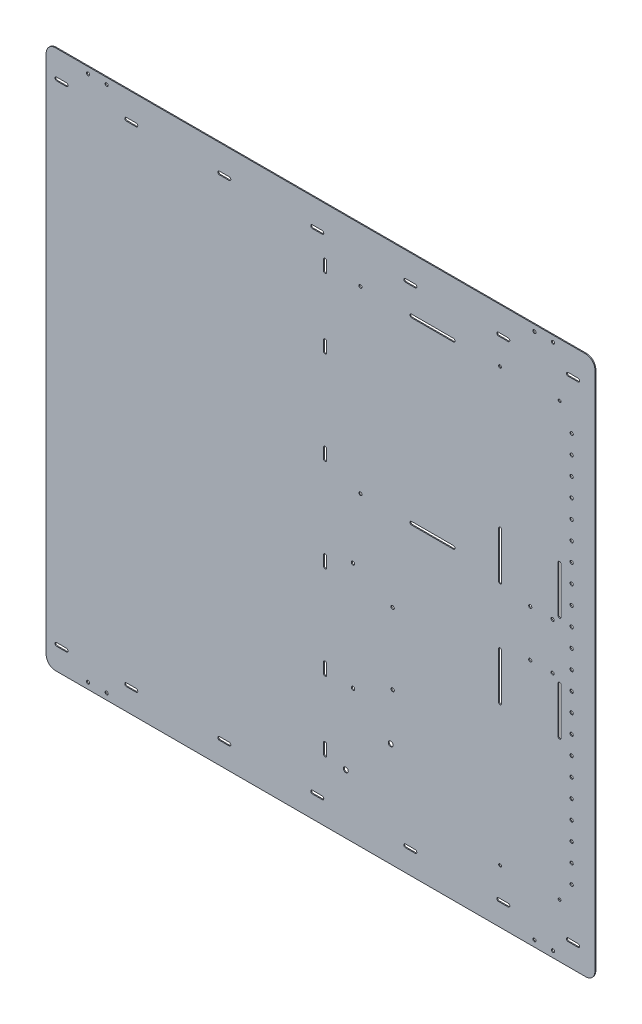
SolidWorks part; units mm, degrees
ref_plane "Front Plane" through (0, 0, 0) normal (0, 0, 1) x (1, 0, 0)
ref_plane "Top Plane" through (0, 0, 0) normal (0, 1, 0) x (1, 0, 0)
ref_plane "Right Plane" through (0, 0, 0) normal (1, 0, 0) x (0, 0, -1)
sketch "Sketch1" plane through (0, 0, 0) normal (0, 0, 1) x (1, 0, 0)
  line L1 (-295, 290) -> (295, 290)
  line L2 (-295, 290) -> (-295, -290)
  line L3 (-295, -290) -> (295, -290)
  line L4 (295, 290) -> (295, -290)
  line L5 (-295, 290) -> (295, -290) construction
  line L6 (-295, -290) -> (295, 290) construction
  point P0 (0, 0)
  dimension "D1" = 590
  dimension "D2" = 580
extrude "Boss-Extrude1" add sketch "Sketch1" along normal blind 1
hole_wizard "M3 Clearance Hole1" positions "Sketch7" profile "Sketch8" hole size "M3" standard "ANSI Metric"
sketch "Sketch7" plane through (0, 0, 0) normal (0, 0, -1) x (-1, 0, 0)
  line L2 (-250, 283.26) -> (250, 283.26)
  line L3 (-250, 283.26) -> (-250, -283.26)
  line L4 (-250, -283.26) -> (250, -283.26)
  line L5 (250, 283.26) -> (250, -283.26)
  line L6 (-250, 283.26) -> (250, -283.26) construction
  line L7 (-250, -283.26) -> (250, 283.26) construction
  line L13 (295, 290) -> (295, -290) construction
  line L14 (-230, -283.26) -> (-230, 283.26)
  line L16 (230, -283.26) -> (230, 283.26)
  point P7 (0, 0)
  point P8 (250, -283.26)
  point P155 (-250, 283.26)
  point P156 (-250, -283.26)
  point P157 (250, 283.26)
  point P212 (-230, 283.26)
  point P215 (-230, -283.26)
  point P218 (230, -283.26)
  point P221 (230, 283.26)
  dimension "D1" = 566.52
  dimension "D2" = 45
  dimension "D3" = 20
  dimension "D4" = 20
sketch "Sketch8" plane through (-230, 283.26, 0) normal (1, 0, 0) x (0, 1, 0)
  line L0 (0, 0) -> (0, 1)
  line L1 (0, 1) -> (1.7, 1)
  line L2 (1.7, 1) -> (1.7, 0.025)
  line L3 (1.7, 0.025) -> (1.725, 0)
  line L5 (1.725, 0) -> (0, 0)
  line L6 (-1.7, 0.025) -> (-1.725, 0) construction
  line L11 (0, -6.35) -> (0, 107.95) construction
  dimension "Thru Hole Dia." = 3.4
  dimension "Thru Hole Depth" = 1
  dimension "Near C'Sink Dia." = 3.45
  dimension "Near C'Sink Angle" = 90
fillet "Fillet1" radius 10 4 edges at (295, -290, 0.5) (-295, -290, 0.5) (-295, 290, 0.5) (295, 290, 0.5)
sketch "Sketch9" plane through (0, 0, 0) normal (0, 0, 1) x (1, 0, 0)
  circle A5 centre (77.5, -126.46) radius 1.8 construction
  circle A6 centre (77.5, -49.96) radius 1.8 construction
  circle A7 centre (34.9, -29.96) radius 1.8 construction
  circle A8 centre (34.9, -146.46) radius 1.8 construction
  circle A9 centre (77.5, -126.46) radius 1.8
  circle A10 centre (77.5, -49.96) radius 1.8
  circle A11 centre (34.9, -29.96) radius 1.8
  circle A12 centre (34.9, -146.46) radius 1.8
extrude "BMS Holes" cut sketch "Sketch9" along normal through all
sketch "Sketch10" plane through (0, 0, 1) normal (0, 0, 1) x (1, 0, 0)
  line L0 (292.75, 264.81) -> (295, 264.81) construction
  line L1 (-208.75, 261.56) -> (-198.25, 261.56) construction
  line L2 (273.25, 263.81) -> (269.75, 263.81)
  line L3 (269.75, 259.31) -> (273.25, 259.31)
  line L4 (-208.75, 263.31) -> (-198.25, 263.31)
  line L5 (-208.75, 259.81) -> (-198.25, 259.81)
  line L6 (-108.75, 261.56) -> (-98.25, 261.56) construction
  line L7 (-108.75, 263.31) -> (-98.25, 263.31)
  line L12 (-108.75, 259.81) -> (-98.25, 259.81)
  line L13 (-8.75, 261.56) -> (1.75, 261.56) construction
  line L14 (-8.75, 263.31) -> (1.75, 263.31)
  line L15 (-8.75, 259.81) -> (1.75, 259.81)
  line L20 (91.25, 261.56) -> (101.75, 261.56) construction
  line L21 (91.25, 263.31) -> (101.75, 263.31)
  line L22 (91.25, 259.81) -> (101.75, 259.81)
  line L23 (191.25, 261.56) -> (201.75, 261.56) construction
  line L28 (191.25, 263.31) -> (201.75, 263.31)
  line L29 (191.25, 259.81) -> (201.75, 259.81)
  line L30 (-108.75, -264.96) -> (-98.25, -264.96) construction
  line L31 (-108.75, -263.21) -> (-98.25, -263.21)
  line L36 (-108.75, -266.71) -> (-98.25, -266.71)
  line L37 (-8.75, -264.96) -> (1.75, -264.96) construction
  line L38 (-8.75, -263.21) -> (1.75, -263.21)
  line L39 (-8.75, -266.71) -> (1.75, -266.71)
  line L44 (91.25, -264.96) -> (101.75, -264.96) construction
  line L45 (91.25, -263.21) -> (101.75, -263.21)
  line L46 (91.25, -266.71) -> (101.75, -266.71)
  line L47 (191.25, -264.96) -> (201.75, -264.96) construction
  line L52 (273.25, 263.81) -> (269.75, 263.81) construction
  line L53 (269.75, 259.31) -> (273.25, 259.31) construction
  line L54 (191.25, -263.21) -> (201.75, -263.21)
  line L55 (191.25, -266.71) -> (201.75, -266.71)
  line L58 (-208.75, -264.96) -> (-198.25, -264.96) construction
  line L59 (-208.75, -263.21) -> (-198.25, -263.21)
  line L62 (-199.75, 264.81) -> (-207.25, 264.81)
  line L63 (-207.25, 258.31) -> (-199.75, 258.31)
  line L64 (-199.75, 264.81) -> (-207.25, 264.81) construction
  line L65 (-207.25, 258.31) -> (-199.75, 258.31) construction
  line L66 (-208.75, -266.71) -> (-198.25, -266.71)
  line L67 (-283.75, 261.56) -> (-273.25, 261.56) construction
  line L70 (-283.75, 263.31) -> (-273.25, 263.31)
  line L71 (-283.75, 259.81) -> (-273.25, 259.81)
  line L74 (100.25, 264.81) -> (92.75, 264.81)
  line L75 (92.75, 258.31) -> (100.25, 258.31)
  line L76 (100.25, 264.81) -> (92.75, 264.81) construction
  line L77 (92.75, 258.31) -> (100.25, 258.31) construction
  line L78 (-208.75, 261.56) -> (-283.75, 261.56) construction
  line L79 (266.25, 261.56) -> (276.75, 261.56) construction
  line L82 (266.25, 263.31) -> (276.75, 263.31)
  line L83 (266.25, 259.81) -> (276.75, 259.81)
  line L86 (200.25, 264.81) -> (192.75, 264.81)
  line L87 (192.75, 258.31) -> (200.25, 258.31)
  line L88 (200.25, 264.81) -> (192.75, 264.81) construction
  line L89 (192.75, 258.31) -> (200.25, 258.31) construction
  line L90 (266.25, -264.96) -> (276.75, -264.96) construction
  line L91 (266.25, -263.21) -> (276.75, -263.21)
  line L94 (266.25, -266.71) -> (276.75, -266.71)
  line L95 (-283.75, -264.96) -> (-273.25, -264.96) construction
  line L98 (-99.75, 264.81) -> (-107.25, 264.81)
  line L99 (-107.25, 258.31) -> (-99.75, 258.31)
  line L100 (-99.75, 264.81) -> (-107.25, 264.81) construction
  line L101 (-107.25, 258.31) -> (-99.75, 258.31) construction
  line L102 (-276.75, 263.81) -> (-280.25, 263.81)
  line L103 (-280.25, 259.31) -> (-276.75, 259.31)
  line L104 (-276.75, 263.81) -> (-280.25, 263.81) construction
  line L105 (-280.25, 259.31) -> (-276.75, 259.31) construction
  line L106 (-283.75, -263.21) -> (-273.25, -263.21)
  line L107 (-283.75, -266.71) -> (-273.25, -266.71)
  line L110 (0.25, 264.81) -> (-7.25, 264.81)
  line L111 (-7.25, 258.31) -> (0.25, 258.31)
  line L112 (0.25, 264.81) -> (-7.25, 264.81) construction
  line L113 (-7.25, 258.31) -> (0.25, 258.31) construction
  line L114 (-283.75, 261.56) -> (266.25, 261.56) construction
  line L115 (4.9, 162.1) -> (4.9, 151.6) construction
  line L118 (6.65, 162.1) -> (6.65, 151.6)
  line L119 (3.15, 162.1) -> (3.15, 151.6)
  line L120 (4.9, 62.1) -> (4.9, 51.6) construction
  line L121 (6.65, 62.1) -> (6.65, 51.6)
  line L122 (3.15, 62.1) -> (3.15, 51.6)
  line L123 (4.9, -37.9) -> (4.9, -48.4) construction
  line L128 (6.65, -37.9) -> (6.65, -48.4)
  line L129 (3.15, -37.9) -> (3.15, -48.4)
  line L130 (4.9, -137.9) -> (4.9, -148.4) construction
  line L131 (6.65, -137.9) -> (6.65, -148.4)
  line L136 (3.15, -137.9) -> (3.15, -148.4)
  line L137 (4.9, 237.1) -> (4.9, 226.6) construction
  line L138 (6.65, 237.1) -> (6.65, 226.6)
  line L139 (3.15, 237.1) -> (3.15, 226.6)
  line L144 (4.9, 162.1) -> (4.9, 237.1) construction
  line L145 (4.9, -212.9) -> (4.9, -223.4) construction
  line L146 (6.65, -212.9) -> (6.65, -223.4)
  line L147 (3.15, -212.9) -> (3.15, -223.4)
  line L152 (4.9, 237.1) -> (4.9, -212.9) construction
  line L178 (-199.75, -261.71) -> (-207.25, -261.71)
  line L179 (-207.25, -268.21) -> (-199.75, -268.21)
  line L180 (-199.75, -261.71) -> (-207.25, -261.71) construction
  line L181 (-207.25, -268.21) -> (-199.75, -268.21) construction
  line L190 (100.25, -261.71) -> (92.75, -261.71)
  line L191 (92.75, -268.21) -> (100.25, -268.21)
  line L192 (100.25, -261.71) -> (92.75, -261.71) construction
  line L193 (92.75, -268.21) -> (100.25, -268.21) construction
  line L202 (200.25, -261.71) -> (192.75, -261.71)
  line L203 (192.75, -268.21) -> (200.25, -268.21)
  line L204 (200.25, -261.71) -> (192.75, -261.71) construction
  line L205 (192.75, -268.21) -> (200.25, -268.21) construction
  line L214 (-99.75, -261.71) -> (-107.25, -261.71)
  line L215 (-107.25, -268.21) -> (-99.75, -268.21)
  line L216 (-99.75, -261.71) -> (-107.25, -261.71) construction
  line L217 (-107.25, -268.21) -> (-99.75, -268.21) construction
  line L218 (-276.75, -262.71) -> (-280.25, -262.71)
  line L219 (-280.25, -267.21) -> (-276.75, -267.21)
  line L220 (-276.75, -262.71) -> (-280.25, -262.71) construction
  line L221 (-280.25, -267.21) -> (-276.75, -267.21) construction
  line L226 (0.25, -261.71) -> (-7.25, -261.71)
  line L227 (-7.25, -268.21) -> (0.25, -268.21)
  line L228 (0.25, -261.71) -> (-7.25, -261.71) construction
  line L229 (-7.25, -268.21) -> (0.25, -268.21) construction
  line L234 (7.15, -219.9) -> (7.15, -216.4)
  line L235 (2.65, -216.4) -> (2.65, -219.9)
  line L276 (7.15, -219.9) -> (7.15, -216.4) construction
  line L277 (2.65, -216.4) -> (2.65, -219.9) construction
  line L290 (8.15, -46.9) -> (8.15, -39.4)
  line L291 (1.65, -39.4) -> (1.65, -46.9)
  line L292 (8.15, -46.9) -> (8.15, -39.4) construction
  line L293 (1.65, -39.4) -> (1.65, -46.9) construction
  line L302 (8.15, -146.9) -> (8.15, -139.4)
  line L303 (1.65, -139.4) -> (1.65, -146.9)
  line L304 (8.15, -146.9) -> (8.15, -139.4) construction
  line L305 (1.65, -139.4) -> (1.65, -146.9) construction
  line L314 (8.15, 153.1) -> (8.15, 160.6)
  line L315 (1.65, 160.6) -> (1.65, 153.1)
  line L316 (8.15, 153.1) -> (8.15, 160.6) construction
  line L317 (1.65, 160.6) -> (1.65, 153.1) construction
  line L322 (8.15, 53.1) -> (8.15, 60.6)
  line L323 (1.65, 60.6) -> (1.65, 53.1)
  line L324 (8.15, 53.1) -> (8.15, 60.6) construction
  line L325 (1.65, 60.6) -> (1.65, 53.1) construction
  line L326 (7.15, 230.1) -> (7.15, 233.6)
  line L327 (2.65, 233.6) -> (2.65, 230.1)
  line L328 (7.15, 230.1) -> (7.15, 233.6) construction
  line L329 (2.65, 233.6) -> (2.65, 230.1) construction
  line L334 (295, 258.31) -> (292.75, 258.31) construction
  line L335 (8.15, -239.4) -> (8.15, -241.65) construction
  line L341 (1.65, -241.65) -> (1.65, -239.4) construction
  line L342 (292.75, -261.71) -> (295, -261.71) construction
  line L348 (295, -268.21) -> (292.75, -268.21) construction
  line L349 (292.75, 264.81) -> (295, 264.81) construction
  line L355 (295, 258.31) -> (292.75, 258.31) construction
  line L356 (8.15, -239.4) -> (8.15, -241.65) construction
  line L362 (1.65, -241.65) -> (1.65, -239.4) construction
  line L363 (292.75, -261.71) -> (295, -261.71) construction
  line L369 (295, -268.21) -> (292.75, -268.21) construction
  arc A0 (292.75, 264.81) -> (292.75, 258.31) centre (292.75, 261.56) ccw construction
  arc A1 (8.15, -239.4) -> (1.65, -239.4) centre (4.9, -239.4) ccw construction
  arc A2 (273.25, 259.31) -> (273.25, 263.81) centre (273.25, 261.56) ccw
  arc A3 (269.75, 263.81) -> (269.75, 259.31) centre (269.75, 261.56) ccw
  arc A4 (-208.75, 263.31) -> (-208.75, 259.81) centre (-208.75, 261.56) ccw
  arc A5 (-198.25, 259.81) -> (-198.25, 263.31) centre (-198.25, 261.56) ccw
  arc A6 (-108.75, 263.31) -> (-108.75, 259.81) centre (-108.75, 261.56) ccw
  arc A7 (-98.25, 259.81) -> (-98.25, 263.31) centre (-98.25, 261.56) ccw
  arc A12 (-8.75, 263.31) -> (-8.75, 259.81) centre (-8.75, 261.56) ccw
  arc A13 (1.75, 259.81) -> (1.75, 263.31) centre (1.75, 261.56) ccw
  arc A14 (91.25, 263.31) -> (91.25, 259.81) centre (91.25, 261.56) ccw
  arc A15 (101.75, 259.81) -> (101.75, 263.31) centre (101.75, 261.56) ccw
  arc A20 (191.25, 263.31) -> (191.25, 259.81) centre (191.25, 261.56) ccw
  arc A21 (201.75, 259.81) -> (201.75, 263.31) centre (201.75, 261.56) ccw
  arc A22 (-108.75, -263.21) -> (-108.75, -266.71) centre (-108.75, -264.96) ccw
  arc A23 (-98.25, -266.71) -> (-98.25, -263.21) centre (-98.25, -264.96) ccw
  arc A28 (-8.75, -263.21) -> (-8.75, -266.71) centre (-8.75, -264.96) ccw
  arc A29 (1.75, -266.71) -> (1.75, -263.21) centre (1.75, -264.96) ccw
  arc A30 (91.25, -263.21) -> (91.25, -266.71) centre (91.25, -264.96) ccw
  arc A31 (101.75, -266.71) -> (101.75, -263.21) centre (101.75, -264.96) ccw
  arc A36 (191.25, -263.21) -> (191.25, -266.71) centre (191.25, -264.96) ccw
  arc A37 (201.75, -266.71) -> (201.75, -263.21) centre (201.75, -264.96) ccw
  arc A38 (-208.75, -263.21) -> (-208.75, -266.71) centre (-208.75, -264.96) ccw
  arc A39 (-198.25, -266.71) -> (-198.25, -263.21) centre (-198.25, -264.96) ccw
  arc A44 (-283.75, 263.31) -> (-283.75, 259.81) centre (-283.75, 261.56) ccw
  arc A45 (-273.25, 259.81) -> (-273.25, 263.31) centre (-273.25, 261.56) ccw
  arc A46 (266.25, 263.31) -> (266.25, 259.81) centre (266.25, 261.56) ccw
  arc A47 (276.75, 259.81) -> (276.75, 263.31) centre (276.75, 261.56) ccw
  arc A52 (273.25, 259.31) -> (273.25, 263.81) centre (273.25, 261.56) ccw construction
  arc A53 (269.75, 263.81) -> (269.75, 259.31) centre (269.75, 261.56) ccw construction
  arc A54 (266.25, -263.21) -> (266.25, -266.71) centre (266.25, -264.96) ccw
  arc A55 (276.75, -266.71) -> (276.75, -263.21) centre (276.75, -264.96) ccw
  arc A58 (-283.75, -263.21) -> (-283.75, -266.71) centre (-283.75, -264.96) ccw
  arc A59 (-273.25, -266.71) -> (-273.25, -263.21) centre (-273.25, -264.96) ccw
  arc A62 (-199.75, 258.31) -> (-199.75, 264.81) centre (-199.75, 261.56) ccw
  arc A63 (-207.25, 264.81) -> (-207.25, 258.31) centre (-207.25, 261.56) ccw
  arc A64 (-199.75, 258.31) -> (-199.75, 264.81) centre (-199.75, 261.56) ccw construction
  arc A65 (-207.25, 264.81) -> (-207.25, 258.31) centre (-207.25, 261.56) ccw construction
  arc A66 (6.65, 162.1) -> (3.15, 162.1) centre (4.9, 162.1) ccw
  arc A67 (3.15, 151.6) -> (6.65, 151.6) centre (4.9, 151.6) ccw
  arc A70 (6.65, 62.1) -> (3.15, 62.1) centre (4.9, 62.1) ccw
  arc A71 (3.15, 51.6) -> (6.65, 51.6) centre (4.9, 51.6) ccw
  arc A74 (100.25, 258.31) -> (100.25, 264.81) centre (100.25, 261.56) ccw
  arc A75 (92.75, 264.81) -> (92.75, 258.31) centre (92.75, 261.56) ccw
  arc A76 (100.25, 258.31) -> (100.25, 264.81) centre (100.25, 261.56) ccw construction
  arc A77 (92.75, 264.81) -> (92.75, 258.31) centre (92.75, 261.56) ccw construction
  arc A78 (6.65, -37.9) -> (3.15, -37.9) centre (4.9, -37.9) ccw
  arc A79 (3.15, -48.4) -> (6.65, -48.4) centre (4.9, -48.4) ccw
  arc A82 (6.65, -137.9) -> (3.15, -137.9) centre (4.9, -137.9) ccw
  arc A83 (3.15, -148.4) -> (6.65, -148.4) centre (4.9, -148.4) ccw
  arc A86 (200.25, 258.31) -> (200.25, 264.81) centre (200.25, 261.56) ccw
  arc A87 (192.75, 264.81) -> (192.75, 258.31) centre (192.75, 261.56) ccw
  arc A88 (200.25, 258.31) -> (200.25, 264.81) centre (200.25, 261.56) ccw construction
  arc A89 (192.75, 264.81) -> (192.75, 258.31) centre (192.75, 261.56) ccw construction
  arc A90 (6.65, 237.1) -> (3.15, 237.1) centre (4.9, 237.1) ccw
  arc A91 (3.15, 226.6) -> (6.65, 226.6) centre (4.9, 226.6) ccw
  arc A94 (6.65, -212.9) -> (3.15, -212.9) centre (4.9, -212.9) ccw
  arc A95 (3.15, -223.4) -> (6.65, -223.4) centre (4.9, -223.4) ccw
  arc A98 (-99.75, 258.31) -> (-99.75, 264.81) centre (-99.75, 261.56) ccw
  arc A99 (-107.25, 264.81) -> (-107.25, 258.31) centre (-107.25, 261.56) ccw
  arc A100 (-99.75, 258.31) -> (-99.75, 264.81) centre (-99.75, 261.56) ccw construction
  arc A101 (-107.25, 264.81) -> (-107.25, 258.31) centre (-107.25, 261.56) ccw construction
  arc A102 (-276.75, 259.31) -> (-276.75, 263.81) centre (-276.75, 261.56) ccw
  arc A103 (-280.25, 263.81) -> (-280.25, 259.31) centre (-280.25, 261.56) ccw
  arc A104 (-276.75, 259.31) -> (-276.75, 263.81) centre (-276.75, 261.56) ccw construction
  arc A105 (-280.25, 263.81) -> (-280.25, 259.31) centre (-280.25, 261.56) ccw construction
  arc A110 (0.25, 258.31) -> (0.25, 264.81) centre (0.25, 261.56) ccw
  arc A111 (-7.25, 264.81) -> (-7.25, 258.31) centre (-7.25, 261.56) ccw
  arc A112 (0.25, 258.31) -> (0.25, 264.81) centre (0.25, 261.56) ccw construction
  arc A113 (-7.25, 264.81) -> (-7.25, 258.31) centre (-7.25, 261.56) ccw construction
  arc A178 (-199.75, -268.21) -> (-199.75, -261.71) centre (-199.75, -264.96) ccw
  arc A179 (-207.25, -261.71) -> (-207.25, -268.21) centre (-207.25, -264.96) ccw
  arc A180 (-199.75, -268.21) -> (-199.75, -261.71) centre (-199.75, -264.96) ccw construction
  arc A181 (-207.25, -261.71) -> (-207.25, -268.21) centre (-207.25, -264.96) ccw construction
  arc A190 (100.25, -268.21) -> (100.25, -261.71) centre (100.25, -264.96) ccw
  arc A191 (92.75, -261.71) -> (92.75, -268.21) centre (92.75, -264.96) ccw
  arc A192 (100.25, -268.21) -> (100.25, -261.71) centre (100.25, -264.96) ccw construction
  arc A193 (92.75, -261.71) -> (92.75, -268.21) centre (92.75, -264.96) ccw construction
  arc A202 (200.25, -268.21) -> (200.25, -261.71) centre (200.25, -264.96) ccw
  arc A203 (192.75, -261.71) -> (192.75, -268.21) centre (192.75, -264.96) ccw
  arc A204 (200.25, -268.21) -> (200.25, -261.71) centre (200.25, -264.96) ccw construction
  arc A205 (192.75, -261.71) -> (192.75, -268.21) centre (192.75, -264.96) ccw construction
  arc A214 (-99.75, -268.21) -> (-99.75, -261.71) centre (-99.75, -264.96) ccw
  arc A215 (-107.25, -261.71) -> (-107.25, -268.21) centre (-107.25, -264.96) ccw
  arc A216 (-99.75, -268.21) -> (-99.75, -261.71) centre (-99.75, -264.96) ccw construction
  arc A217 (-107.25, -261.71) -> (-107.25, -268.21) centre (-107.25, -264.96) ccw construction
  arc A218 (-276.75, -267.21) -> (-276.75, -262.71) centre (-276.75, -264.96) ccw
  arc A219 (-280.25, -262.71) -> (-280.25, -267.21) centre (-280.25, -264.96) ccw
  arc A220 (-276.75, -267.21) -> (-276.75, -262.71) centre (-276.75, -264.96) ccw construction
  arc A221 (-280.25, -262.71) -> (-280.25, -267.21) centre (-280.25, -264.96) ccw construction
  arc A226 (0.25, -268.21) -> (0.25, -261.71) centre (0.25, -264.96) ccw
  arc A227 (-7.25, -261.71) -> (-7.25, -268.21) centre (-7.25, -264.96) ccw
  arc A228 (0.25, -268.21) -> (0.25, -261.71) centre (0.25, -264.96) ccw construction
  arc A229 (-7.25, -261.71) -> (-7.25, -268.21) centre (-7.25, -264.96) ccw construction
  arc A234 (2.65, -219.9) -> (7.15, -219.9) centre (4.9, -219.9) ccw
  arc A235 (7.15, -216.4) -> (2.65, -216.4) centre (4.9, -216.4) ccw
  arc A276 (2.65, -219.9) -> (7.15, -219.9) centre (4.9, -219.9) ccw construction
  arc A277 (7.15, -216.4) -> (2.65, -216.4) centre (4.9, -216.4) ccw construction
  arc A290 (1.65, -46.9) -> (8.15, -46.9) centre (4.9, -46.9) ccw
  arc A291 (8.15, -39.4) -> (1.65, -39.4) centre (4.9, -39.4) ccw
  arc A292 (1.65, -46.9) -> (8.15, -46.9) centre (4.9, -46.9) ccw construction
  arc A293 (8.15, -39.4) -> (1.65, -39.4) centre (4.9, -39.4) ccw construction
  arc A302 (1.65, -146.9) -> (8.15, -146.9) centre (4.9, -146.9) ccw
  arc A303 (8.15, -139.4) -> (1.65, -139.4) centre (4.9, -139.4) ccw
  arc A304 (1.65, -146.9) -> (8.15, -146.9) centre (4.9, -146.9) ccw construction
  arc A305 (8.15, -139.4) -> (1.65, -139.4) centre (4.9, -139.4) ccw construction
  arc A314 (1.65, 153.1) -> (8.15, 153.1) centre (4.9, 153.1) ccw
  arc A315 (8.15, 160.6) -> (1.65, 160.6) centre (4.9, 160.6) ccw
  arc A316 (1.65, 153.1) -> (8.15, 153.1) centre (4.9, 153.1) ccw construction
  arc A317 (8.15, 160.6) -> (1.65, 160.6) centre (4.9, 160.6) ccw construction
  arc A322 (1.65, 53.1) -> (8.15, 53.1) centre (4.9, 53.1) ccw
  arc A323 (8.15, 60.6) -> (1.65, 60.6) centre (4.9, 60.6) ccw
  arc A324 (1.65, 53.1) -> (8.15, 53.1) centre (4.9, 53.1) ccw construction
  arc A325 (8.15, 60.6) -> (1.65, 60.6) centre (4.9, 60.6) ccw construction
  arc A326 (2.65, 230.1) -> (7.15, 230.1) centre (4.9, 230.1) ccw
  arc A327 (7.15, 233.6) -> (2.65, 233.6) centre (4.9, 233.6) ccw
  arc A328 (2.65, 230.1) -> (7.15, 230.1) centre (4.9, 230.1) ccw construction
  arc A329 (7.15, 233.6) -> (2.65, 233.6) centre (4.9, 233.6) ccw construction
  arc A330 (292.75, -261.71) -> (292.75, -268.21) centre (292.75, -264.96) ccw construction
  arc A331 (292.75, 264.81) -> (292.75, 258.31) centre (292.75, 261.56) ccw construction
  arc A332 (8.15, -239.4) -> (1.65, -239.4) centre (4.9, -239.4) ccw construction
  arc A333 (292.75, -261.71) -> (292.75, -268.21) centre (292.75, -264.96) ccw construction
  point P3 (-203.5, 261.56)
  point P12 (-103.5, 261.56)
  point P19 (-3.5, 261.56)
  point P26 (96.5, 261.56)
  point P33 (196.5, 261.56)
  point P40 (-103.5, -264.96)
  point P47 (-3.5, -264.96)
  point P54 (96.5, -264.96)
  point P61 (196.5, -264.96)
  point P69 (-203.5, -264.96)
  point P76 (-278.5, 261.56)
  point P88 (4.9, 156.85)
  point P90 (271.5, 261.56)
  point P102 (271.5, -264.96)
  point P115 (-278.5, -264.96)
  point P134 (4.9, 231.85)
  point P136 (4.9, 56.85)
  point P144 (4.9, -43.15)
  point P164 (4.9, -143.15)
  point P183 (4.9, -218.15)
  dimension "D8" = 3.5
  dimension "D9" = 5
  dimension "D12" = 2
  dimension "D21" = 4
  dimension "D23" = 2
  dimension "D14" = 75
  dimension "D18" = 550
  dimension "D24" = 75
  dimension "D26" = 450
  dimension "D7" = 0
  dimension "D10" = 0
  dimension "D11" = 2
  dimension "D13" = 0
  dimension "D15" = 2
  dimension "D16" = 0
  dimension "D17" = 2
  dimension "D19" = 0
  dimension "D20" = 0
  dimension "D22" = 0
  dimension "D25" = 2
  dimension "D33" = 0
  dimension "D36" = 0
  dimension "D39" = 0
  dimension "D42" = 0
  dimension "D43" = 0
  dimension "D45" = 0
  dimension "D52" = 0
  dimension "D56" = 0
  dimension "D59" = 0
  dimension "D62" = 0
  dimension "D64" = 0
  dimension "D65" = 0
extrude "Wire Duct Holes" cut sketch "Sketch10" against normal through all
sketch "Sketch12" plane through (0, 0, 0) normal (0, 0, -1) x (-1, 0, 0)
  circle A8 centre (-249.5, -25) radius 1.7 construction
  circle A9 centre (-225.5, -25) radius 1.7 construction
  circle A10 centre (-249.5, 25) radius 1.7 construction
  circle A11 centre (-225.5, 25) radius 1.7 construction
  circle A12 centre (-249.5, -25) radius 1.7
  circle A13 centre (-225.5, -25) radius 1.7
  circle A14 centre (-249.5, 25) radius 1.7
  circle A15 centre (-225.5, 25) radius 1.7
extrude "Remote Stop Holes" cut sketch "Sketch12" against normal through all
sketch "Sketch13" plane through (0, 0, 0) normal (0, 0, -1) x (-1, 0, 0)
  line L0 (-257, 31.26) -> (-257, 81.26) construction
  line L1 (-295, -280) -> (-295, 280) construction
  line L2 (-258.5, 31.26) -> (-258.5, 81.26)
  line L3 (-255.5, 31.26) -> (-255.5, 81.26)
  line L4 (-193, 31.26) -> (-193, 81.26) construction
  line L5 (-194.5, 31.26) -> (-194.5, 81.26)
  line L6 (0, 0) -> (-295, 0) construction
  line L7 (-191.5, 31.26) -> (-191.5, 81.26)
  line L8 (-193, -31.26) -> (-193, -81.26) construction
  line L9 (-194.5, -31.26) -> (-194.5, -81.26)
  line L10 (-191.5, -31.26) -> (-191.5, -81.26)
  line L11 (-257, -31.26) -> (-257, -81.26) construction
  line L12 (-258.5, -31.26) -> (-258.5, -81.26)
  line L13 (-255.5, -31.26) -> (-255.5, -81.26)
  circle A8 centre (-257, 232.26) radius 1.5 construction
  circle A9 centre (-193, 232.26) radius 1.5 construction
  circle A10 centre (-193, 31.26) radius 1.5 construction
  circle A11 centre (-257, 31.26) radius 1.5 construction
  circle A12 centre (-257, 232.26) radius 1.5
  circle A13 centre (-193, 232.26) radius 1.5
  circle A14 centre (-193, 31.26) radius 1.5 construction
  circle A15 centre (-257, 31.26) radius 1.5 construction
  circle A16 centre (-257, -31.26) radius 1.5 construction
  circle A17 centre (-193, -31.26) radius 1.5 construction
  circle A18 centre (-193, -232.26) radius 1.5
  circle A19 centre (-257, -232.26) radius 1.5
  arc A20 (-258.5, 31.26) -> (-255.5, 31.26) centre (-257, 31.26) ccw
  arc A21 (-255.5, 81.26) -> (-258.5, 81.26) centre (-257, 81.26) ccw
  arc A22 (-194.5, 31.26) -> (-191.5, 31.26) centre (-193, 31.26) ccw
  arc A23 (-191.5, 81.26) -> (-194.5, 81.26) centre (-193, 81.26) ccw
  arc A24 (-194.5, -31.26) -> (-191.5, -31.26) centre (-193, -31.26) cw
  arc A25 (-191.5, -81.26) -> (-194.5, -81.26) centre (-193, -81.26) cw
  arc A26 (-258.5, -31.26) -> (-255.5, -31.26) centre (-257, -31.26) cw
  arc A27 (-255.5, -81.26) -> (-258.5, -81.26) centre (-257, -81.26) cw
  point P27 (-257, 56.26)
  point P33 (-193, 56.26)
  point P40 (-193, -56.26)
  point P46 (-257, -56.26)
  dimension "D1" = 50
extrude "Motor Driver Stack Holes" cut sketch "Sketch13" against normal through all
sketch "Sketch14" plane through (0, 0, 0) normal (0, 0, -1) x (-1, 0, 0)
  line L0 (-142.9, 233.44) -> (-97.9, 233.44)
  line L1 (-142.9, 230.04) -> (-97.9, 230.04)
  line L2 (-142.9, 40.44) -> (-97.9, 40.44)
  line L3 (-97.9, 37.04) -> (-142.9, 37.04)
  circle A0 centre (-97.9, 38.74) radius 1.7 construction
  circle A1 centre (-42.9, 38.74) radius 1.7 construction
  circle A2 centre (-42.9, 231.74) radius 1.7 construction
  circle A3 centre (-97.9, 231.74) radius 1.7 construction
  circle A4 centre (-142.9, 231.74) radius 1.7 construction
  circle A5 centre (-142.9, 38.74) radius 1.7 construction
  arc A6 (-97.9, 37.04) -> (-97.9, 40.44) centre (-97.9, 38.74) ccw
  circle A7 centre (-42.9, 38.74) radius 1.7
  circle A8 centre (-42.9, 231.74) radius 1.7
  arc A9 (-97.9, 230.04) -> (-97.9, 233.44) centre (-97.9, 231.74) ccw
  arc A10 (-142.9, 233.44) -> (-142.9, 230.04) centre (-142.9, 231.74) ccw
  arc A11 (-142.9, 40.44) -> (-142.9, 37.04) centre (-142.9, 38.74) ccw
extrude "Power Cube Holes" cut sketch "Sketch14" against normal through all
sketch "Sketch16" plane through (0, 0, 0) normal (0, 0, -1) x (-1, 0, 0)
  line L0 (-295, 290) -> (-295, -290) construction
  line L1 (-270, -211.7) -> (-270, -244.96) construction
  line L2 (-295, -244.96) -> (295, -244.96) construction
  line L3 (-270, 208.3) -> (-270, 241.56) construction
  line L4 (-295, 241.56) -> (295, 241.56) construction
  circle A0 centre (-270, -211.7) radius 1.75
  circle A1 centre (-270, -191.7) radius 1.75
  circle A2 centre (-270, -171.7) radius 1.75
  circle A3 centre (-270, -151.7) radius 1.75
  circle A4 centre (-270, -131.7) radius 1.75
  circle A5 centre (-270, -111.7) radius 1.75
  circle A6 centre (-270, -91.7) radius 1.75
  circle A7 centre (-270, -71.7) radius 1.75
  circle A8 centre (-270, -51.7) radius 1.75
  circle A9 centre (-270, -31.7) radius 1.75
  circle A10 centre (-270, -11.7) radius 1.75
  circle A11 centre (-270, 8.3) radius 1.75
  circle A12 centre (-270, 28.3) radius 1.75
  circle A13 centre (-270, 48.3) radius 1.75
  circle A14 centre (-270, 68.3) radius 1.75
  circle A15 centre (-270, 88.3) radius 1.75
  circle A16 centre (-270, 108.3) radius 1.75
  circle A17 centre (-270, 128.3) radius 1.75
  circle A18 centre (-270, 148.3) radius 1.75
  circle A19 centre (-270, 168.3) radius 1.75
  circle A20 centre (-270, 188.3) radius 1.75
  circle A21 centre (-270, 208.3) radius 1.75
  dimension "D1" = 3.5
  dimension "D3" = 22
  dimension "D4" = 20
  dimension "D2" = 25
extrude "Flex Holes" cut sketch "Sketch16" against normal through all
sketch "Sketch17" plane through (0, 0, 0) normal (0, 0, -1) x (-1, 0, 0)
  circle A0 centre (-75.5, -177.9448) radius 2.65 construction
  circle A1 centre (-27.1862, -226.2586) radius 2.65 construction
  circle A2 centre (-75.5, -177.9448) radius 2.65
  circle A3 centre (-27.1862, -226.2586) radius 2.65
extrude "Cut-Extrude3" cut sketch "Sketch17" against normal through all
